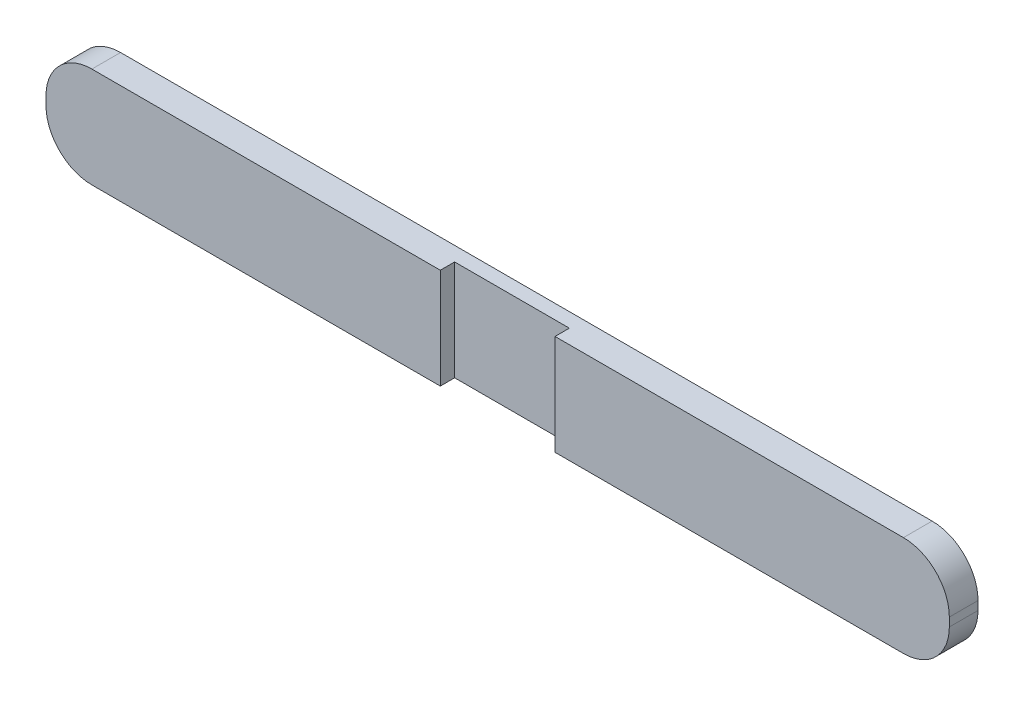
SolidWorks part; units mm, degrees
ref_plane "Front Plane" through (0, 0, 0) normal (0, 0, 1) x (1, 0, 0)
ref_plane "Top Plane" through (0, 0, 0) normal (0, 1, 0) x (1, 0, 0)
ref_plane "Right Plane" through (0, 0, 0) normal (1, 0, 0) x (0, 0, -1)
sketch "Sketch2" plane through (0, 0, 0) normal (0, 0, 1) x (1, 0, 0)
  line L1 (-16.7384, 1.7966) -> (28.1878, 1.7966)
  line L2 (-19.2784, -0.7434) -> (-19.2784, -1.2197)
  line L3 (-16.7384, -3.7597) -> (28.1878, -3.7597)
  line L4 (30.7278, -0.7434) -> (30.7278, -1.2197)
  arc A0 (30.7278, -0.7434) -> (28.1878, 1.7966) centre (28.1878, -0.7434) ccw
  arc A1 (28.1878, -3.7597) -> (30.7278, -1.2197) centre (28.1878, -1.2197) ccw
  arc A2 (-19.2784, -1.2197) -> (-16.7384, -3.7597) centre (-16.7384, -1.2197) ccw
  arc A3 (-19.2784, -0.7434) -> (-16.7384, 1.7966) centre (-16.7384, -0.7434) cw
  point P6 (30.7278, 1.7966)
  point P9 (30.7278, -3.7597)
  dimension "D3" = 2.54
  dimension "D1" = 50.0062
  dimension "D2" = 5.5562
extrude "Boss-Extrude1" add sketch "Sketch2" along normal blind 1.5875
sketch "Sketch3" plane through (0, 0, 1.5875) normal (0, 0, 1) x (1, 0, 0)
  line L1 (8.8997, 1.7966) -> (2.5497, 1.7966)
  line L2 (8.8997, 1.7966) -> (8.8997, -3.7597)
  line L3 (8.8997, -3.7597) -> (2.5497, -3.7597)
  line L4 (2.5497, 1.7966) -> (2.5497, -3.7597)
  line L5 (28.1878, 1.7966) -> (-16.7384, 1.7966) construction
  line L6 (-16.7384, -3.7597) -> (28.1878, -3.7597) construction
  point P6 (5.7247, 1.7966)
  point P8 (5.7247, 1.7966)
  dimension "D1" = 6.35
extrude "Cut-Extrude1" cut sketch "Sketch3" against normal blind 0.7937
